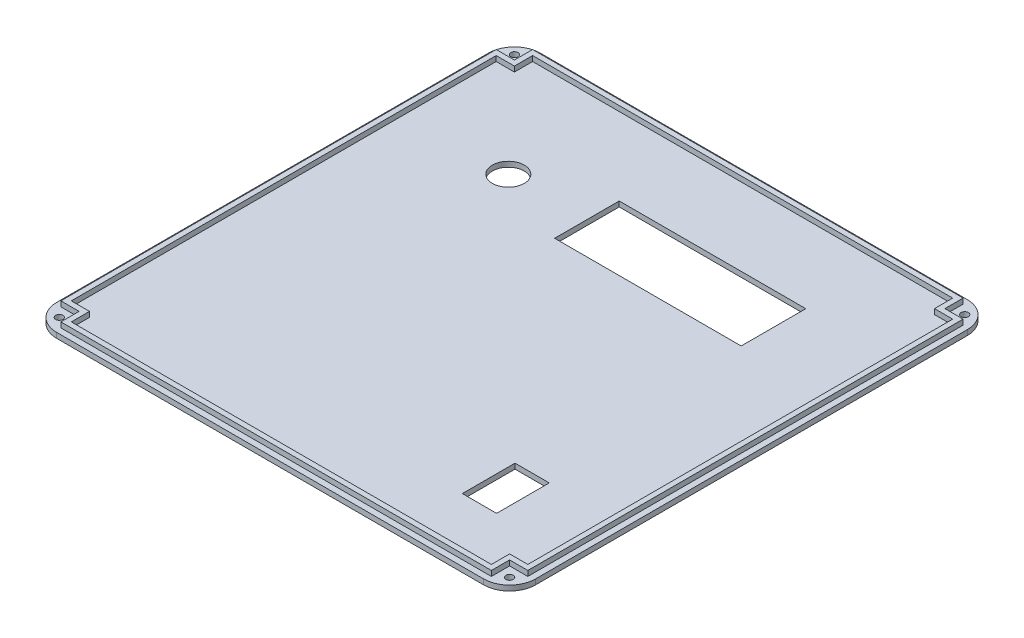
SolidWorks part; units mm, degrees
ref_plane "Front Plane" through (0, 0, 0) normal (0, 0, 1) x (1, 0, 0)
ref_plane "Top Plane" through (0, 0, 0) normal (0, 1, 0) x (1, 0, 0)
ref_plane "Right Plane" through (0, 0, 0) normal (1, 0, 0) x (0, 0, -1)
sketch "Sketch1" plane through (0, 0, 0) normal (0, 1, 0) x (1, 0, 0)
  line L0 (-92, 92.92) -> (-92, -92.92)
  line L1 (-83, 90.92) -> (83, 90.92) construction
  line L2 (-90, 83.92) -> (-90, -83.92) construction
  line L3 (-83, -90.92) -> (83, -90.92) construction
  line L4 (90, 83.92) -> (90, -83.92) construction
  line L5 (-90, 90.92) -> (90, -90.92) construction
  line L6 (-90, -90.92) -> (90, 90.92) construction
  line L7 (-92, -92.92) -> (92, -92.92)
  line L8 (92, 92.92) -> (92, -92.92)
  line L9 (-92, 92.92) -> (92, 92.92)
  line L10 (-57.851, 69.7) -> (-63.041, 69.7) construction
  line L11 (-80.326, 0.92) -> (29.534, 0.92) construction
  line L12 (-80.326, 0.92) -> (-80.326, -75.92) construction
  line L13 (-80.326, -75.92) -> (29.534, -75.92) construction
  line L14 (29.534, 0.92) -> (29.534, -75.92) construction
  line L15 (34.534, 0.92) -> (80.234, 0.92) construction
  line L16 (34.534, 0.92) -> (34.534, -62.18) construction
  line L17 (34.534, -62.18) -> (80.234, -62.18) construction
  line L18 (80.234, 0.92) -> (80.234, -62.18) construction
  line L19 (-80.326, 46.52) -> (-2.026, 46.52) construction
  line L20 (-80.326, 46.52) -> (-80.326, 8.92) construction
  line L21 (-80.326, 8.92) -> (-2.026, 8.92) construction
  line L22 (-2.026, 46.52) -> (-2.026, 8.92) construction
  line L23 (-63.041, 72.7) -> (-19.311, 72.7) construction
  line L24 (-63.041, 72.7) -> (-63.041, 51.52) construction
  line L25 (-63.041, 51.52) -> (-19.311, 51.52) construction
  line L26 (-19.311, 72.7) -> (-19.311, 51.52) construction
  line L27 (17.234, 80.92) -> (78.234, 80.92) construction
  line L28 (17.234, 80.92) -> (17.234, 22.92) construction
  line L29 (17.234, 22.92) -> (78.234, 22.92) construction
  line L30 (78.234, 80.92) -> (78.234, 22.92) construction
  line L31 (-24.511, 54.52) -> (-19.311, 54.52) construction
  line L32 (23.734, 74.42) -> (72.2367, 26.9227) construction
  line L33 (17.234, 74.42) -> (78.234, 74.42) construction
  line L34 (57.384, 0.92) -> (57.384, -4.08) construction
  line L35 (57.384, -8.96) -> (57.384, -75.267) construction
  line L36 (57.384, -58.45) -> (57.384, -62.18) construction
  line L37 (54.944, -54.01) -> (54.944, -56.01)
  line L38 (59.824, -54.01) -> (59.824, -56.01)
  line L39 (-50.026, -24.01) -> (-80.326, -24.01) construction
  line L40 (-48.776, -22.76) -> (-48.776, 0.92) construction
  line L41 (-12.616, -52.48) -> (-12.616, -75.92) construction
  line L42 (-11.366, -51.23) -> (29.534, -51.23) construction
  line L43 (15.234, 82.92) -> (15.234, 20.92) construction
  line L44 (15.234, 20.92) -> (80.234, 20.92) construction
  line L45 (80.234, 82.92) -> (80.234, 20.92) construction
  line L46 (15.234, 82.92) -> (80.234, 82.92) construction
  line L47 (-41.176, 72.7) -> (-41.176, 51.52) construction
  line L48 (-80.626, 46.82) -> (-80.626, 8.62) construction
  line L51 (-90, 83.92) -> (-83, 83.92) construction
  line L52 (-83, 90.92) -> (-83, 83.92) construction
  line L55 (90, 83.92) -> (83, 83.92) construction
  line L56 (83, 90.92) -> (83, 83.92) construction
  line L59 (-90, -83.92) -> (-83, -83.92) construction
  line L60 (-83, -90.92) -> (-83, -83.92) construction
  line L63 (90, -83.92) -> (83, -83.92) construction
  line L64 (83, -90.92) -> (83, -83.92) construction
  line L65 (-80.626, 8.62) -> (-1.726, 8.62) construction
  line L66 (-1.726, 46.82) -> (-1.726, 8.62) construction
  line L67 (-80.626, 46.82) -> (-1.726, 46.82) construction
  line L68 (-80.626, 39.8852) -> (-82.626, 39.8852)
  line L69 (-82.626, 39.8852) -> (-82.626, 48.82)
  line L70 (-82.626, 48.82) -> (-73.6912, 48.82)
  line L71 (-73.6912, 48.82) -> (-73.6912, 46.82)
  line L72 (-73.6912, 46.82) -> (-80.626, 46.82)
  line L73 (-80.626, 46.82) -> (-80.626, 39.8852)
  line L74 (-1.726, 15.5548) -> (0.274, 15.5548)
  line L75 (0.274, 15.5548) -> (0.274, 6.62)
  line L76 (0.274, 6.62) -> (-8.6608, 6.62)
  line L77 (-8.6608, 6.62) -> (-8.6608, 8.62)
  line L78 (-8.6608, 8.62) -> (-1.726, 8.62)
  line L79 (-1.726, 8.62) -> (-1.726, 15.5548)
  line L80 (-90, 90.92) -> (90, 90.92) construction
  line L81 (-90, 90.92) -> (-90, -90.92) construction
  line L82 (90, 90.92) -> (90, -90.92) construction
  line L83 (-90, -90.92) -> (90, -90.92) construction
  line L84 (-82.7, -90.62) -> (82.7, -90.62)
  line L85 (82.7, -90.62) -> (82.7, -83.62)
  line L86 (89.7, -83.62) -> (82.7, -83.62)
  line L87 (89.7, 83.62) -> (89.7, -83.62)
  line L88 (89.7, 83.62) -> (82.7, 83.62)
  line L89 (82.7, 90.62) -> (82.7, 83.62)
  line L90 (-82.7, 90.62) -> (82.7, 90.62)
  line L91 (-82.7, 90.62) -> (-82.7, 83.62)
  line L92 (-89.7, 83.62) -> (-82.7, 83.62)
  line L93 (-89.7, 83.62) -> (-89.7, -83.62)
  line L94 (-89.7, -83.62) -> (-82.7, -83.62)
  line L95 (-82.7, -90.62) -> (-82.7, -83.62)
  line L96 (-80.7, -88.62) -> (80.7, -88.62)
  line L97 (80.7, -88.62) -> (80.7, -81.62)
  line L98 (87.7, -81.62) -> (80.7, -81.62)
  line L99 (87.7, 81.62) -> (87.7, -81.62)
  line L100 (87.7, 81.62) -> (80.7, 81.62)
  line L101 (80.7, 88.62) -> (80.7, 81.62)
  line L102 (-80.7, 88.62) -> (80.7, 88.62)
  line L103 (-80.7, 88.62) -> (-80.7, 81.62)
  line L104 (-87.7, 81.62) -> (-80.7, 81.62)
  line L105 (-87.7, 81.62) -> (-87.7, -81.62)
  line L106 (-87.7, -81.62) -> (-80.7, -81.62)
  line L107 (-80.7, -88.62) -> (-80.7, -81.62)
  line L109 (-83, 83.92) -> (-90, 83.92)
  line L110 (-83, 83.92) -> (-83, 90.92)
  line L111 (-83, 90.92) -> (-90, 90.92)
  line L112 (-90, 83.92) -> (-90, 90.92)
  line L113 (83, 83.92) -> (90, 83.92)
  line L114 (83, 83.92) -> (83, 90.92)
  line L115 (83, 90.92) -> (90, 90.92)
  line L116 (90, 83.92) -> (90, 90.92)
  line L117 (83, -83.92) -> (90, -83.92)
  line L118 (83, -83.92) -> (83, -90.92)
  line L119 (83, -90.92) -> (90, -90.92)
  line L120 (90, -83.92) -> (90, -90.92)
  line L121 (-83, -83.92) -> (-90, -83.92)
  line L122 (-83, -83.92) -> (-83, -90.92)
  line L123 (-83, -90.92) -> (-90, -90.92)
  line L124 (-90, -83.92) -> (-90, -90.92)
  circle A0 centre (-56.451, 69.7) radius 1.4
  circle A1 centre (-25.911, 54.52) radius 1.4
  circle A2 centre (23.734, 74.42) radius 0.9
  circle A3 centre (72.2367, 26.9227) radius 0.9
  circle A4 centre (57.384, -6.52) radius 2.44
  arc A5 (54.944, -56.01) -> (59.824, -56.01) centre (57.384, -56.01) ccw
  arc A6 (59.824, -54.01) -> (54.944, -54.01) centre (57.384, -54.01) ccw
  circle A7 centre (-48.776, -24.01) radius 1.25
  circle A8 centre (-12.616, -51.23) radius 1.25
  point P0 (0, 0)
  dimension "D4" = 2.8
  dimension "D11" = 1.8
  dimension "D22" = 4.88
  dimension "D23" = 2
  dimension "D26" = 2.5
  dimension "D2" = 21.18
  dimension "D3" = 43.73
  dimension "D5" = 5.19
  dimension "D6" = 5.2
  dimension "D7" = 3
  dimension "D8" = 3
  dimension "D9" = 61
  dimension "D10" = 58
  dimension "D12" = 44.4
  dimension "D13" = 67.886
  dimension "D14" = 6.5
  dimension "D15" = 6.5
  dimension "D16" = 37.6
  dimension "D17" = 78.3
  dimension "D18" = 63.1
  dimension "D19" = 45.7
  dimension "D20" = 5
  dimension "D21" = 3.73
  dimension "D24" = 109.86
  dimension "D25" = 76.84
  dimension "D27" = 23.44
  dimension "D28" = 40.9
  dimension "D29" = 23.68
  dimension "D30" = 30.3
  dimension "D32" = 5
  dimension "D33" = 8
  dimension "D34" = 5
  dimension "D35" = 15
  dimension "D36" = 8
  dimension "D37" = 20
  dimension "D38" = 180
  dimension "D39" = 7
  dimension "D41" = 9.674
  dimension "D42" = 2
  dimension "D43" = 0.3
  dimension "D1" = 2
  dimension "D31" = 2
  dimension "D40" = 0.3
  dimension "D44" = 2
extrude "Boss-Extrude1" add sketch "Sketch1" along normal blind 2 contours L95 L84 L85 L86 L87 L88 L89 L90 L91 L92 L93 L94 L96 L107 L106 L105 L104 L103 L102 L101 L100 L99 L98 L97 | L52 L51 | L56 L55 | L60 L59 | L64 L63
sketch "Sketch13" plane through (0, 0, 0) normal (0, -1, 0) x (1, 0, 0)
  line L0 (-90, -87.42) -> (-83, -87.42) construction
  line L1 (83, -87.42) -> (90, -87.42) construction
  line L2 (54.944, 56.01) -> (54.944, 54.01)
  line L3 (59.824, 54.01) -> (59.824, 56.01)
  line L4 (-92, 92.92) -> (-92, -92.92)
  line L5 (92, 92.92) -> (-92, 92.92)
  line L6 (92, -92.92) -> (92, 92.92)
  line L7 (-92, -92.92) -> (92, -92.92)
  line L8 (-92, 92.92) -> (-92, -92.92)
  line L9 (92, 92.92) -> (-92, 92.92)
  line L10 (92, -92.92) -> (92, 92.92)
  line L11 (-92, -92.92) -> (92, -92.92)
  line L12 (54.944, 56.01) -> (54.944, 54.01)
  line L13 (59.824, 54.01) -> (59.824, 56.01)
  line L14 (83, 87.42) -> (90, 87.42) construction
  line L15 (-90, 87.42) -> (-83, 87.42) construction
  line L16 (90, -83.92) -> (83, -83.92)
  line L17 (90, -90.92) -> (90, -83.92)
  line L18 (83, -90.92) -> (90, -90.92)
  line L19 (83, -83.92) -> (83, -90.92)
  line L20 (90, -83.92) -> (83, -83.92)
  line L21 (90, -90.92) -> (90, -83.92)
  line L22 (83, -90.92) -> (90, -90.92)
  line L23 (83, -83.92) -> (83, -90.92)
  line L24 (-83, -83.92) -> (-90, -83.92)
  line L25 (-90, -83.92) -> (-90, -90.92)
  line L26 (-90, -90.92) -> (-83, -90.92)
  line L27 (-83, -90.92) -> (-83, -83.92)
  line L28 (-83, -83.92) -> (-90, -83.92)
  line L29 (-90, -83.92) -> (-90, -90.92)
  line L30 (-90, -90.92) -> (-83, -90.92)
  line L31 (-83, -90.92) -> (-83, -83.92)
  line L32 (-90, 83.92) -> (-83, 83.92)
  line L33 (-83, 83.92) -> (-83, 90.92)
  line L34 (-83, 90.92) -> (-90, 90.92)
  line L35 (-90, 90.92) -> (-90, 83.92)
  line L36 (-90, 83.92) -> (-83, 83.92)
  line L37 (-83, 83.92) -> (-83, 90.92)
  line L38 (-83, 90.92) -> (-90, 90.92)
  line L39 (-90, 90.92) -> (-90, 83.92)
  line L40 (83, 83.92) -> (90, 83.92)
  line L41 (90, 83.92) -> (90, 90.92)
  line L42 (90, 90.92) -> (83, 90.92)
  line L43 (83, 90.92) -> (83, 83.92)
  line L44 (83, 83.92) -> (90, 83.92)
  line L45 (90, 83.92) -> (90, 90.92)
  line L46 (90, 90.92) -> (83, 90.92)
  line L47 (83, 90.92) -> (83, 83.92)
  line L50 (-1.726, -15.5548) -> (0.274, -15.5548)
  line L51 (0.274, -15.5548) -> (0.274, -6.62)
  line L52 (0.274, -6.62) -> (-8.6608, -6.62)
  line L53 (-8.6608, -6.62) -> (-8.6608, -8.62)
  line L54 (-8.6608, -8.62) -> (-1.726, -8.62)
  line L55 (-1.726, -8.62) -> (-1.726, -15.5548)
  line L56 (-1.726, -15.5548) -> (0.274, -15.5548)
  line L57 (0.274, -15.5548) -> (0.274, -6.62)
  line L58 (0.274, -6.62) -> (-8.6608, -6.62)
  line L59 (-8.6608, -6.62) -> (-8.6608, -8.62)
  line L60 (-8.6608, -8.62) -> (-1.726, -8.62)
  line L61 (-1.726, -8.62) -> (-1.726, -15.5548)
  line L62 (-73.6912, -48.82) -> (-73.6912, -46.82)
  line L63 (-82.626, -48.82) -> (-73.6912, -48.82)
  line L64 (-82.626, -39.8852) -> (-82.626, -48.82)
  line L65 (-80.626, -39.8852) -> (-82.626, -39.8852)
  line L66 (-80.626, -46.82) -> (-80.626, -39.8852)
  line L67 (-73.6912, -46.82) -> (-80.626, -46.82)
  line L68 (-73.6912, -48.82) -> (-73.6912, -46.82)
  line L69 (-82.626, -48.82) -> (-73.6912, -48.82)
  line L70 (-82.626, -39.8852) -> (-82.626, -48.82)
  line L71 (-80.626, -39.8852) -> (-82.626, -39.8852)
  line L72 (-80.626, -46.82) -> (-80.626, -39.8852)
  line L73 (-73.6912, -46.82) -> (-80.626, -46.82)
  line L80 (80.7, 88.62) -> (-80.7, 88.62)
  line L81 (80.7, 81.62) -> (80.7, 88.62)
  line L82 (87.7, 81.62) -> (80.7, 81.62)
  line L83 (87.7, -81.62) -> (87.7, 81.62)
  line L84 (80.7, -81.62) -> (87.7, -81.62)
  line L85 (80.7, -88.62) -> (80.7, -81.62)
  line L86 (-80.7, -88.62) -> (80.7, -88.62)
  line L87 (-80.7, -81.62) -> (-80.7, -88.62)
  line L88 (-87.7, -81.62) -> (-80.7, -81.62)
  line L89 (-87.7, 81.62) -> (-87.7, -81.62)
  line L90 (-80.7, 81.62) -> (-87.7, 81.62)
  line L91 (-80.7, 88.62) -> (-80.7, 81.62)
  line L92 (80.7, 88.62) -> (-80.7, 88.62)
  line L93 (80.7, 81.62) -> (80.7, 88.62)
  line L94 (87.7, 81.62) -> (80.7, 81.62)
  line L95 (87.7, -81.62) -> (87.7, 81.62)
  line L96 (80.7, -81.62) -> (87.7, -81.62)
  line L97 (80.7, -88.62) -> (80.7, -81.62)
  line L98 (-80.7, -88.62) -> (80.7, -88.62)
  line L99 (-80.7, -81.62) -> (-80.7, -88.62)
  line L100 (-87.7, -81.62) -> (-80.7, -81.62)
  line L101 (-87.7, 81.62) -> (-87.7, -81.62)
  line L102 (-80.7, 81.62) -> (-87.7, 81.62)
  line L103 (-80.7, 88.62) -> (-80.7, 81.62)
  line L104 (-89.7, 83.62) -> (-89.7, -83.62)
  line L105 (-82.7, 83.62) -> (-89.7, 83.62)
  line L106 (-82.7, 90.62) -> (-82.7, 83.62)
  line L107 (82.7, 90.62) -> (-82.7, 90.62)
  line L108 (82.7, 83.62) -> (82.7, 90.62)
  line L109 (89.7, 83.62) -> (82.7, 83.62)
  line L110 (89.7, -83.62) -> (89.7, 83.62)
  line L111 (82.7, -83.62) -> (89.7, -83.62)
  line L112 (82.7, -90.62) -> (82.7, -83.62)
  line L113 (-82.7, -90.62) -> (82.7, -90.62)
  line L114 (-82.7, -83.62) -> (-82.7, -90.62)
  line L115 (-89.7, -83.62) -> (-82.7, -83.62)
  line L116 (-89.7, 83.62) -> (-89.7, -83.62)
  line L117 (-82.7, 83.62) -> (-89.7, 83.62)
  line L118 (-82.7, 90.62) -> (-82.7, 83.62)
  line L119 (82.7, 90.62) -> (-82.7, 90.62)
  line L120 (82.7, 83.62) -> (82.7, 90.62)
  line L121 (89.7, 83.62) -> (82.7, 83.62)
  line L122 (89.7, -83.62) -> (89.7, 83.62)
  line L123 (82.7, -83.62) -> (89.7, -83.62)
  line L124 (82.7, -90.62) -> (82.7, -83.62)
  line L125 (-82.7, -90.62) -> (82.7, -90.62)
  line L126 (-82.7, -83.62) -> (-82.7, -90.62)
  line L127 (-89.7, -83.62) -> (-82.7, -83.62)
  circle A0 centre (-86.5, -87.42) radius 1.4
  circle A1 centre (-56.451, -69.7) radius 1.4
  circle A2 centre (-56.451, -69.7) radius 1.4
  circle A3 centre (57.384, 6.52) radius 2.44
  circle A4 centre (57.384, 6.52) radius 2.44
  circle A5 centre (72.2367, -26.9227) radius 0.9
  circle A6 centre (72.2367, -26.9227) radius 0.9
  circle A7 centre (23.734, -74.42) radius 0.9
  circle A8 centre (23.734, -74.42) radius 0.9
  circle A9 centre (-25.911, -54.52) radius 1.4
  circle A10 centre (-25.911, -54.52) radius 1.4
  circle A11 centre (-12.616, 51.23) radius 1.25
  circle A12 centre (-12.616, 51.23) radius 1.25
  circle A13 centre (-48.776, 24.01) radius 1.25
  circle A14 centre (-48.776, 24.01) radius 1.25
  circle A15 centre (86.5, -87.42) radius 1.4
  arc A16 (59.824, 56.01) -> (54.944, 56.01) centre (57.384, 56.01) ccw
  arc A17 (54.944, 54.01) -> (59.824, 54.01) centre (57.384, 54.01) ccw
  arc A18 (59.824, 56.01) -> (54.944, 56.01) centre (57.384, 56.01) ccw
  arc A19 (54.944, 54.01) -> (59.824, 54.01) centre (57.384, 54.01) ccw
  circle A20 centre (86.5, 87.42) radius 1.4
  circle A21 centre (-86.5, 87.42) radius 1.4
  dimension "D18" = 2.8
  dimension "D1" = 0
  dimension "D2" = 0
  dimension "D3" = 0
  dimension "D4" = 0
  dimension "D5" = 0
  dimension "D6" = 0
  dimension "D7" = 0
  dimension "D8" = 0
  dimension "D9" = 0
  dimension "D10" = 0
  dimension "D11" = 0
  dimension "D12" = 0
  dimension "D13" = 0
  dimension "D14" = 0
  dimension "D15" = 0
  dimension "D16" = 0
  dimension "D17" = 0
extrude "Boss-Extrude6" add sketch "Sketch13" along normal blind 2 contours A0 | A15 | A20 | A21 | L11 L10 L9 L8
fillet "Fillet3" radius 10 4 edges at (-92, -1, 92.92) (92, -1, 92.92) (92, -1, -92.92) (-92, -1, -92.92)
sketch "Sketch14" plane through (0, -2, 0) normal (0, -1, 0) x (1, 0, 0)
  line L0 (92, 0) -> (-92, 0) construction
  line L1 (92, -82.92) -> (92, 82.92) construction
  line L2 (-92, 82.92) -> (-92, -82.92) construction
  line L3 (0, 0) -> (0, -92.92) construction
  line L4 (-82, -92.92) -> (82, -92.92) construction
  line L5 (92, -46.46) -> (53.9945, -46.46) construction
  line L6 (53.6945, -58.57) -> (53.6945, -34.35) construction
  line L11 (53.6945, -34.35) -> (-17.3755, -34.35) construction
  line L12 (-17.3755, -58.57) -> (-17.3755, -34.35) construction
  line L13 (53.6945, -58.57) -> (-17.3755, -58.57) construction
  line L14 (53.9945, -58.87) -> (53.9945, -34.05)
  line L15 (53.9945, -34.05) -> (-17.6755, -34.05)
  line L16 (-17.6755, -58.87) -> (-17.6755, -34.05)
  line L17 (53.9945, -58.87) -> (-17.6755, -58.87)
  line L18 (53.9945, -58.87) -> (53.9945, -69.1895) construction
  line L19 (53.6945, -46.46) -> (-53.6945, -46.46) construction
  line L20 (-53.9945, -46.46) -> (-92, -46.46) construction
  line L21 (62.7, 48.38) -> (62.7, 68.62)
  line L26 (62.4, 48.68) -> (49.84, 48.68) construction
  line L27 (62.4, 48.68) -> (62.4, 68.32) construction
  line L28 (62.4, 68.32) -> (49.84, 68.32) construction
  line L29 (49.84, 48.68) -> (49.84, 68.32) construction
  line L30 (62.4, 48.68) -> (49.84, 68.32) construction
  line L31 (62.4, 68.32) -> (49.84, 48.68) construction
  line L32 (62.7, 68.62) -> (49.54, 68.62)
  line L33 (49.54, 48.38) -> (49.54, 68.62)
  line L34 (62.7, 48.38) -> (49.54, 48.38)
  line L39 (-80.7, 88.62) -> (-80.7, 81.62)
  line L40 (80.7, 88.62) -> (-80.7, 88.62)
  line L41 (80.7, 81.62) -> (80.7, 88.62)
  line L42 (87.7, 81.62) -> (80.7, 81.62)
  line L43 (87.7, -81.62) -> (87.7, 81.62)
  line L44 (80.7, -81.62) -> (87.7, -81.62)
  line L45 (80.7, -88.62) -> (80.7, -81.62)
  line L46 (-80.7, -88.62) -> (80.7, -88.62)
  line L47 (-80.7, -81.62) -> (-80.7, -88.62)
  line L48 (-87.7, -81.62) -> (-80.7, -81.62)
  line L49 (-87.7, 81.62) -> (-87.7, -81.62)
  line L50 (-80.7, 81.62) -> (-87.7, 81.62)
  line L51 (-80.7, 88.62) -> (-80.7, 81.62) construction
  line L52 (80.7, 88.62) -> (-80.7, 88.62) construction
  line L53 (80.7, 81.62) -> (80.7, 88.62) construction
  line L54 (87.7, 81.62) -> (80.7, 81.62) construction
  line L55 (87.7, -81.62) -> (87.7, 81.62) construction
  line L56 (80.7, -81.62) -> (87.7, -81.62) construction
  line L57 (80.7, -88.62) -> (80.7, -81.62) construction
  line L58 (-80.7, -88.62) -> (80.7, -88.62) construction
  line L59 (-80.7, -81.62) -> (-80.7, -88.62) construction
  line L60 (-87.7, -81.62) -> (-80.7, -81.62) construction
  line L61 (-87.7, 81.62) -> (-87.7, -81.62) construction
  line L62 (-80.7, 81.62) -> (-87.7, 81.62) construction
  circle A0 centre (-47.8745, -46.46) radius 5.82 construction
  circle A1 centre (-47.8745, -46.46) radius 6.12
  point P29 (56.12, 58.5)
  dimension "D1" = 11.64
  dimension "D4" = 71.07
  dimension "D5" = 24.22
  dimension "D6" = 0.3
  dimension "D7" = 20
  dimension "D9" = 25
  dimension "D10" = 12.56
  dimension "D11" = 19.64
  dimension "D2" = 0.3
  dimension "D3" = 0.3
  dimension "D8" = 0
extrude "Cut-Extrude9" cut sketch "Sketch14" against normal up to next
